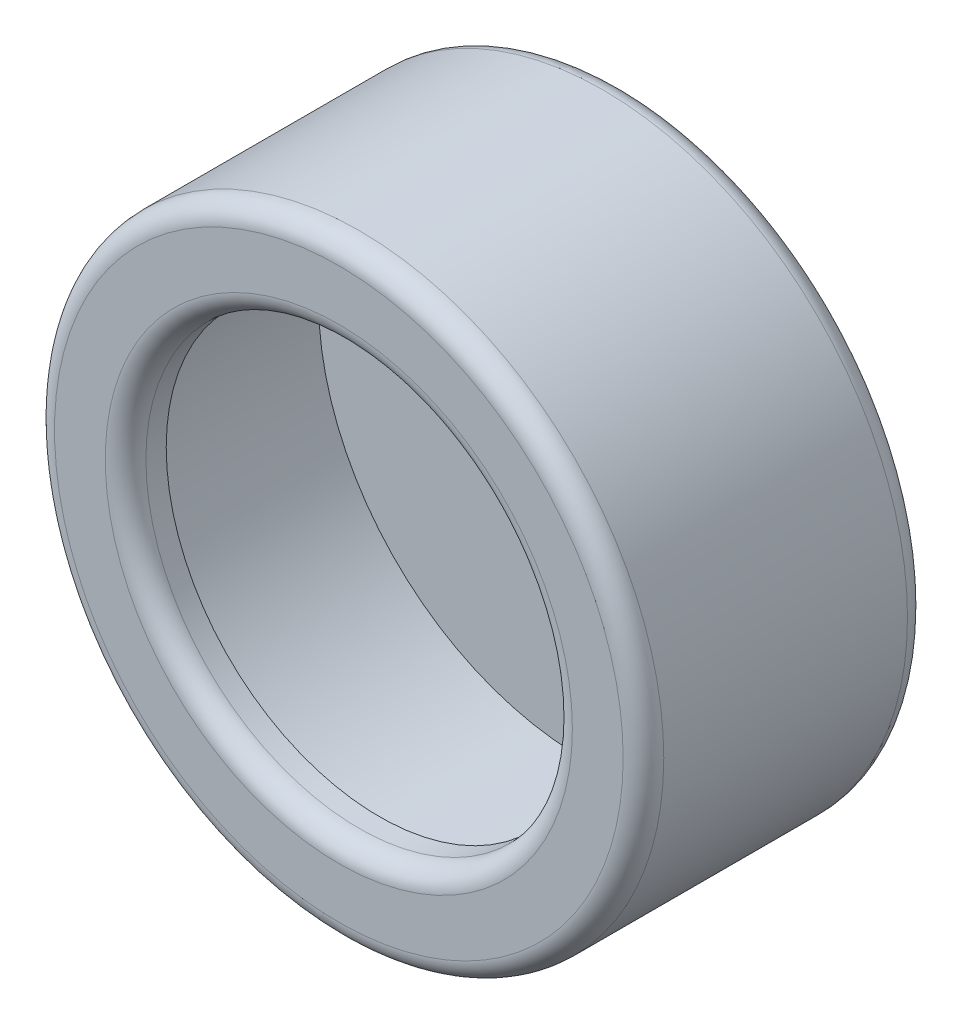
SolidWorks part; units mm, degrees
ref_plane "Front" through (0, 0, 0) normal (0, 0, 1) x (1, 0, 0)
ref_plane "Top" through (0, 0, 0) normal (0, 1, 0) x (1, 0, 0)
ref_plane "Right" through (0, 0, 0) normal (1, 0, 0) x (0, 0, -1)
sketch "草图1" plane through (0, 0, 0) normal (0, 0, 1) x (1, 0, 0)
  circle A0 centre (0, 0) radius 7.5
  dimension "D1" = 15
extrude "凸台-拉伸1" add sketch "草图1" along normal blind 7
sketch "草图2" plane through (0, 0, 7) normal (0, 0, 1) x (1, 0, 0)
  circle A0 centre (0, 0) radius 5.25
  dimension "D1" = 10.5
extrude "切除-拉伸1" cut sketch "草图2" against normal blind 6
sketch "草图3" plane through (0, 0, 1) normal (0, 0, 1) x (1, 0, 0)
  circle A0 centre (0, 0) radius 6.5
  dimension "D1" = 13
extrude "切除-拉伸2" cut sketch "草图3" along normal blind 5
fillet "圆角1" radius 0.5 3 edges at (7.5, 0, 0) (5.25, 0, 7) (7.5, 0, 7)
